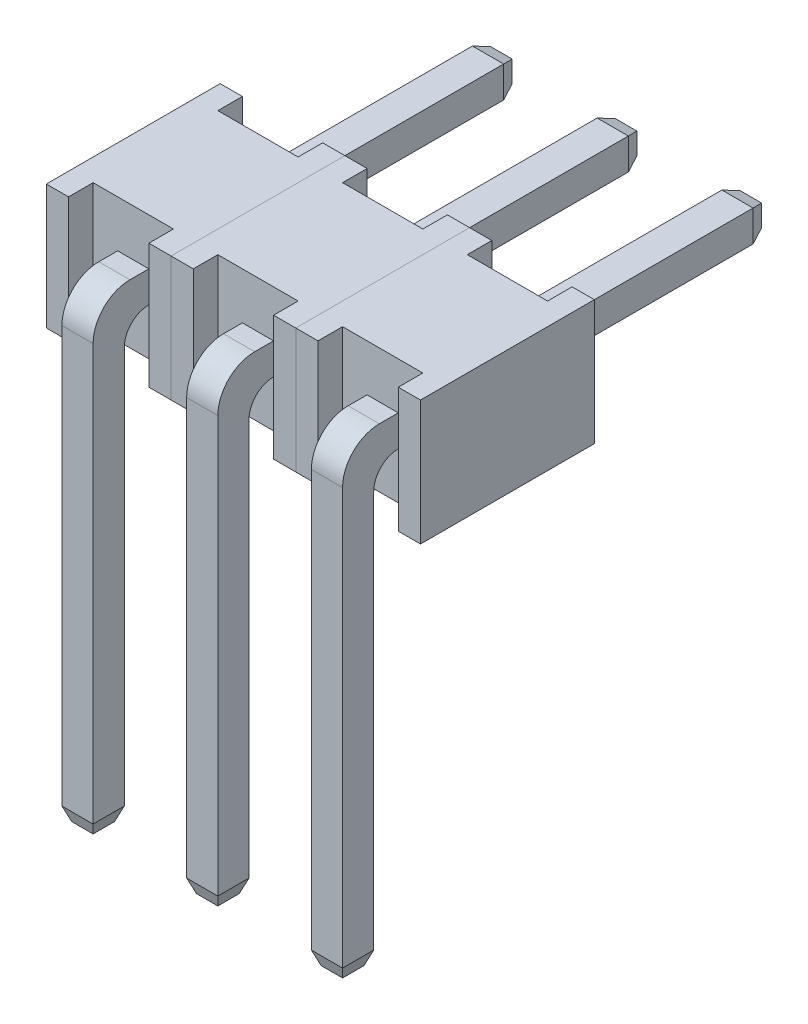
SolidWorks part; units mm, degrees
ref_plane "Front Plane" through (0, 0, 0) normal (0, 0, 1) x (1, 0, 0)
ref_plane "Top Plane" through (0, 0, 0) normal (0, 1, 0) x (1, 0, 0)
ref_plane "Right Plane" through (0, 0, 0) normal (1, 0, 0) x (0, 0, -1)
sketch "Sketch1" plane through (0, 0, 0) normal (0, 0, 1) x (1, 0, 0)
  line L0 (2.54, 10.4525) -> (2.54, 7.9125) construction
  line L1 (0, 10.4525) -> (13.2523, 10.4525)
  line L2 (0, 10.4525) -> (0, 7.9125)
  line L3 (0, 7.9125) -> (13.2523, 7.9125)
  line L4 (13.2523, 10.4525) -> (13.2523, 7.9125)
  line L5 (1.5875, 9.5) -> (0.9525, 9.5)
  line L6 (1.5875, 9.5) -> (1.5875, 0)
  line L7 (1.5875, 0) -> (0.9525, 0)
  line L8 (0.9525, 9.5) -> (0.9525, 0)
  line L9 (3.4925, 9.5) -> (4.1275, 9.5)
  line L10 (3.4925, 9.5) -> (3.4925, 0)
  line L11 (3.4925, 0) -> (4.1275, 0)
  line L12 (4.1275, 9.5) -> (4.1275, 0)
  line L14 (0.9525, 8.865) -> (1.5875, 8.865)
  line L15 (0.9525, 8.865) -> (0.9525, 9.5)
  line L16 (0.9525, 9.5) -> (1.5875, 9.5)
  line L17 (1.5875, 8.865) -> (1.5875, 9.5)
  line L18 (0.9525, 8.865) -> (1.5875, 9.5) construction
  line L19 (0.9525, 9.5) -> (1.5875, 8.865) construction
  point P12 (1.27, 9.5)
  point P16 (1.27, 9.1825)
  point P22 (0, 9.1825)
  dimension "D1" = 0.635
  dimension "D2" = 2.54
  dimension "D3" = 2.54
  dimension "D4" = 1.27
  dimension "D5" = 2.54
  dimension "D6" = 9.5
sketch "Sketch2" plane through (0, 0, 0) normal (0, 0, 1) x (1, 0, 0)
  line L1 (0.9525, 0) -> (1.5875, 0)
  line L2 (0.9525, 0) -> (0.9525, 9.5)
  line L3 (0.9525, 9.5) -> (1.5875, 9.5)
  line L4 (1.5875, 0) -> (1.5875, 9.5)
extrude "Boss-Extrude1" add sketch "Sketch2" against normal blind 0.635
sketch "Sketch3" plane through (0, 0, -0.635) normal (0, 0, -1) x (-1, 0, 0)
  line L0 (-1.5875, 0) -> (-1.5875, 9.5) construction
  line L1 (-0.9525, 9.5) -> (-1.5875, 9.5)
  line L2 (-0.9525, 9.5) -> (-0.9525, 8.865)
  line L3 (-0.9525, 8.865) -> (-1.5875, 8.865)
  line L4 (-1.5875, 9.5) -> (-1.5875, 8.865)
extrude "Boss-Extrude2" add sketch "Sketch3" along normal blind 8
fillet "Fillet1" radius 0.5 1 edges at (1.27, 8.865, -0.635)
fillet "Fillet2" radius 0.75 1 edges at (1.27, 9.5, 0)
sketch "Sketch4" plane through (0, 0, -0.635) normal (0, 0, -1) x (-1, 0, 0)
  line L0 (0, 7.9125) -> (-13.2523, 7.9125) construction
  line L1 (0, 10.4525) -> (-0.4525, 10.4525)
  line L2 (0, 10.4525) -> (0, 7.9125)
  line L3 (0, 7.9125) -> (-0.4525, 7.9125)
  line L4 (-0.4525, 10.4525) -> (-0.4525, 7.9125)
  line L5 (-0.9525, 9.5) -> (-0.9525, 0) construction
  line L6 (-2.54, 10.4525) -> (-2.0875, 10.4525)
  line L7 (-2.54, 10.4525) -> (-2.54, 7.9125)
  line L8 (-2.54, 7.9125) -> (-2.0875, 7.9125)
  line L9 (-2.0875, 10.4525) -> (-2.0875, 7.9125)
  dimension "D1" = 0.5
extrude "Boss-Extrude3" add sketch "Sketch4" along normal blind 0.5 separate body
sketch "Sketch5" plane through (0, 0, -1.135) normal (0, 0, -1) x (-1, 0, 0)
  line L1 (-2.54, 10.4525) -> (0, 10.4525)
  line L2 (-2.54, 10.4525) -> (-2.54, 7.9125)
  line L3 (-2.54, 7.9125) -> (0, 7.9125)
  line L4 (0, 10.4525) -> (0, 7.9125)
extrude "Boss-Extrude4" add sketch "Sketch5" along normal blind 2.54
sketch "Sketch6" plane through (0, 0, -3.675) normal (0, 0, -1) x (-1, 0, 0)
  line L1 (-0.4525, 10.4525) -> (0, 10.4525)
  line L2 (-0.4525, 10.4525) -> (-0.4525, 7.9125)
  line L3 (-0.4525, 7.9125) -> (0, 7.9125)
  line L4 (0, 10.4525) -> (0, 7.9125)
  line L5 (-2.0875, 10.4525) -> (-2.54, 10.4525)
  line L6 (-2.0875, 10.4525) -> (-2.0875, 7.9125)
  line L7 (-2.0875, 7.9125) -> (-2.54, 7.9125)
  line L8 (-2.54, 10.4525) -> (-2.54, 7.9125)
extrude "Boss-Extrude5" add sketch "Sketch6" along normal blind 0.5
chamfer "Chamfer1" distance 0.1 angle 70 4 edges at (0.9525, 9.1825, -8.635) (1.27, 9.5, -8.635) (1.5875, 9.1825, -8.635) (1.27, 8.865, -8.635)
chamfer "Chamfer2" distance 0.1 angle 70 4 edges at (1.27, 0, 0) (1.5875, 0, -0.3175) (0.9525, 0, -0.3175) (1.27, 0, -0.635)
pattern_linear "Num pins" count 3 spacing 2.54 along (1, 0, 0) of bodies 106
